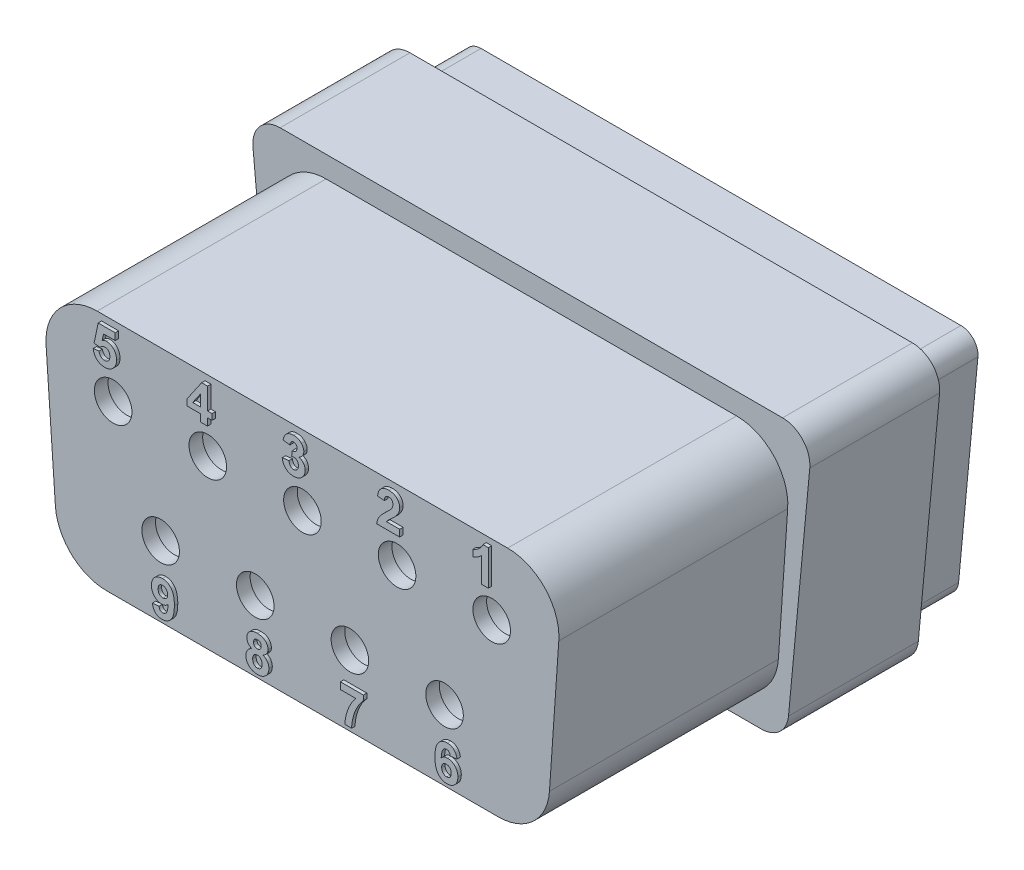
SolidWorks part; units mm, degrees
ref_plane "Front Plane" through (0, 0, 0) normal (0, 0, 1) x (1, 0, 0)
ref_plane "Top Plane" through (0, 0, 0) normal (0, 1, 0) x (1, 0, 0)
ref_plane "Right Plane" through (0, 0, 0) normal (1, 0, 0) x (0, 0, -1)
sketch "Sketch1" plane through (0, 0, 0) normal (0, 0, 1) x (1, 0, 0)
  line L0 (-7.3524, 4.1) -> (-7.3524, -7.0187) construction
  line L1 (7.3524, 4.1) -> (7.3524, -6.7915) construction
  line L4 (0, 4.1) -> (0, -4.1) construction
  line L5 (-15.42, 0) -> (15.42, 0) construction
  line L12 (7.5263, -3.3751) -> (8.1489, 3.2249)
  line L13 (-6.7298, -4.1) -> (6.7298, -4.1)
  line L14 (-8.1489, 3.2249) -> (-7.5263, -3.3751)
  line L15 (7.3524, 4.1) -> (-7.3524, 4.1)
  arc A12 (8.1489, 3.2249) -> (7.3524, 4.1) centre (7.3524, 3.3) ccw
  arc A13 (6.7298, -4.1) -> (7.5263, -3.3751) centre (6.7298, -3.3) ccw
  arc A14 (-7.5263, -3.3751) -> (-6.7298, -4.1) centre (-6.7298, -3.3) ccw
  arc A15 (-7.3524, 4.1) -> (-8.1489, 3.2249) centre (-7.3524, 3.3) ccw
  point P4 (0, 0)
  dimension "D4" = 0.8
  dimension "D1" = 16.2978
  dimension "D2" = 15.0525
  dimension "D3" = 8.2
  dimension "D5" = 4.1
  dimension "D6" = 7.5263
  dimension "D7" = 7.3524
  dimension "D8" = 5.389
  dimension "D9" = 7.3524
  dimension "D10" = 5.389
extrude "Boss-Extrude1" add sketch "Sketch1" along normal blind 3.8
sketch "Sketch2" plane through (0, 0, 0) normal (0, 0, -1) x (-1, 0, 0)
  line L0 (-9.3074, 0) -> (9.3074, 0) construction
  line L1 (0, 6.7455) -> (0, -6.1309) construction
  line L2 (-5.8958, 3.5) -> (5.8958, 3.5) construction
  line L11 (6.9289, -3.3188) -> (7.5516, 3.2812)
  line L12 (-6.7298, -3.5) -> (6.7298, -3.5)
  line L13 (7.3524, 3.5) -> (-7.3524, 3.5)
  line L14 (-7.5516, 3.2812) -> (-6.9289, -3.3188)
  line L15 (6.9546, -3.047) -> (7.5206, 2.953)
  line L16 (-6.4568, -3.5) -> (6.4568, -3.5)
  line L17 (7.0228, 3.5) -> (-7.0228, 3.5)
  line L18 (-7.5206, 2.953) -> (-6.9546, -3.047)
  arc A4 (7.5206, 2.953) -> (7.0228, 3.5) centre (7.0228, 3) ccw
  arc A5 (6.9546, -3.047) -> (6.4568, -3.5) centre (6.4568, -3) cw
  arc A6 (-6.9546, -3.047) -> (-6.4568, -3.5) centre (-6.4568, -3) ccw
  arc A7 (-7.5206, 2.953) -> (-7.0228, 3.5) centre (-7.0228, 3) cw
  arc A8 (7.5516, 3.2812) -> (7.3524, 3.5) centre (7.3524, 3.3) ccw
  arc A9 (6.7298, -3.5) -> (6.9289, -3.3188) centre (6.7298, -3.3) ccw
  arc A10 (-7.3524, 3.5) -> (-7.5516, 3.2812) centre (-7.3524, 3.3) ccw
  arc A11 (-6.9289, -3.3188) -> (-6.7298, -3.5) centre (-6.7298, -3.3) ccw
  point P2 (0, 0)
  point P8 (0, 3.5)
  dimension "D3" = 0.5
  dimension "D1" = 3.5
  dimension "D2" = 0.6
extrude "Boss-Extrude2" add sketch "Sketch2" along normal blind 1.75
sketch "Sketch3" plane through (0, 0, -1.75) normal (0, 0, -1) x (-1, 0, 0)
  line L0 (-7.8447, 0) -> (7.8447, 0) construction
  line L1 (-7.5263, -3.3751) -> (-8.1489, 3.2249) construction
  line L2 (8.1489, 3.2249) -> (7.5263, -3.3751) construction
  line L3 (7.5206, 2.953) -> (7.5206, -6.4358) construction
  line L4 (-7.5206, 2.953) -> (-7.5206, -5.6245) construction
  line L5 (2.77, 1.42) -> (5.54, 1.42) construction
  line L6 (4.155, 1.42) -> (4.155, -5.9419) construction
  circle A0 centre (5.54, 1.42) radius 0.5
  circle A1 centre (2.77, 1.42) radius 0.5
  circle A2 centre (0, 1.42) radius 0.5
  circle A3 centre (-2.77, 1.42) radius 0.5
  circle A4 centre (-5.54, 1.42) radius 0.5
  circle A5 centre (4.1506, -1.42) radius 0.5
  circle A6 centre (1.3806, -1.42) radius 0.5
  circle A7 centre (-1.3894, -1.42) radius 0.5
  circle A8 centre (-4.1594, -1.42) radius 0.5
  dimension "D2" = 1
  dimension "D14" = 1
  dimension "D1" = 1.9806
  dimension "D3" = 1.42
  dimension "D5" = 2.77
  dimension "D6" = 2.77
  dimension "D7" = 2.77
  dimension "D8" = 2.77
  dimension "D9" = 1.9806
  dimension "D10" = 3.3656
  dimension "D11" = 3.37
  dimension "D12" = 4
  dimension "D13" = 1.42
  dimension "D15" = 1.42
  dimension "D4" = 5
extrude "Cut-Extrude1" cut sketch "Sketch3" against normal up to surface (5.55 mm away) up to face at (0, -0.0321, 3.8)
sketch "Sketch6" plane through (0, 0, -1.75) normal (0, 0, -1) x (-1, 0, 0)
  line L0 (-7.4543, 2.25) -> (7.4543, 2.25) construction
  line L1 (-7.5206, 2.953) -> (-6.9546, -3.047) construction
  line L2 (6.9546, -3.047) -> (7.5206, 2.953) construction
  line L3 (7.0228, 3.5) -> (-7.0228, 3.5) construction
  line L4 (-6.9307, -3.3) -> (6.9307, -3.3) construction
  line L5 (-7.5206, 2.953) -> (-6.9546, -3.047) construction
  line L6 (-6.4568, -3.5) -> (6.4568, -3.5) construction
  text T0 "    1     2     3     4     5" font "Arial" height in points 4
  text T1 "      6     7     8     9" font "Arial" height in points 4
  dimension "D1" = 1.25
  dimension "D2" = 0.2
extrude "Boss-Extrude4" add sketch "Sketch6" along normal blind 0.1
ref_plane "Plane2" through (0, 0, 2.05) normal (0, 0, 1) x (1, 0, 0)
sketch "Sketch8" plane through (0, 0, 2.05) normal (0, 0, 1) x (1, 0, 0)
  circle A0 centre (-5.54, 1.42) radius 0.75
  circle A1 centre (-2.77, 1.42) radius 0.75
  circle A2 centre (0, 1.42) radius 0.75
  circle A3 centre (2.77, 1.42) radius 0.75
  circle A4 centre (5.54, 1.42) radius 0.75
  circle A5 centre (4.1594, -1.42) radius 0.75
  circle A6 centre (1.3894, -1.42) radius 0.75
  circle A7 centre (-1.3806, -1.42) radius 0.75
  circle A8 centre (-4.1506, -1.42) radius 0.75
  dimension "D1" = 1.5
extrude "Cut-Extrude3" cut sketch "Sketch8" against normal up to surface (3.8 mm away) up to face at (-4.099, -2.884, -1.75)
sketch "Sketch9" plane through (0, 0, 3.8) normal (0, 0, 1) x (1, 0, 0)
  line L0 (-7.5033, 1.8715) -> (-7.23, -2.0785)
  line L1 (-5.7336, -3.475) -> (5.7336, -3.475)
  line L2 (7.23, -2.0785) -> (7.5033, 1.8715)
  line L3 (6.0069, 3.475) -> (-6.0069, 3.475)
  line L4 (0, 3.475) -> (0, -3.475) construction
  line L5 (-7.3666, -0.1035) -> (7.3666, -0.1035) construction
  arc A0 (-7.23, -2.0785) -> (-5.7336, -3.475) centre (-5.7336, -1.975) ccw
  arc A1 (5.7336, -3.475) -> (7.23, -2.0785) centre (5.7336, -1.975) ccw
  arc A2 (7.5033, 1.8715) -> (6.0069, 3.475) centre (6.0069, 1.975) ccw
  arc A3 (-6.0069, 3.475) -> (-7.5033, 1.8715) centre (-6.0069, 1.975) ccw
  circle A4 centre (-5.54, 1.42) radius 0.5 construction
  circle A5 centre (-2.77, 1.42) radius 0.5 construction
  circle A6 centre (0, 1.42) radius 0.5 construction
  circle A7 centre (2.77, 1.42) radius 0.5 construction
  circle A8 centre (5.54, 1.42) radius 0.5 construction
  circle A9 centre (4.1594, -1.42) radius 0.5 construction
  circle A10 centre (1.3894, -1.42) radius 0.5 construction
  circle A11 centre (-1.3806, -1.42) radius 0.5 construction
  circle A12 centre (-4.1506, -1.42) radius 0.5 construction
  circle A13 centre (-5.54, 1.42) radius 0.5
  circle A14 centre (-2.77, 1.42) radius 0.5
  circle A15 centre (0, 1.42) radius 0.5
  circle A16 centre (2.77, 1.42) radius 0.5
  circle A17 centre (5.54, 1.42) radius 0.5
  circle A18 centre (4.1594, -1.42) radius 0.5
  circle A19 centre (1.3894, -1.42) radius 0.5
  circle A20 centre (-1.3806, -1.42) radius 0.5
  circle A21 centre (-4.1506, -1.42) radius 0.5
  dimension "D5" = 1.5
extrude "Boss-Extrude5" add sketch "Sketch9" along normal blind 6.7
sketch "Sketch10" plane through (0, 0, 10.5) normal (0, 0, 1) x (1, 0, 0)
  line L0 (-8.0522, 2.275) -> (8.0522, 2.275) construction
  line L1 (-7.5334, -3.275) -> (7.5334, -3.275) construction
  line L2 (0, 4.1751) -> (0, -4.0249) construction
  line L3 (-7.8376, 0) -> (7.8376, 0) construction
  line L4 (6.0069, 3.475) -> (-6.0069, 3.475) construction
  line L5 (-5.7336, -3.475) -> (5.7336, -3.475) construction
  text T0 "     5     4     3     2     1" font "Arial" height in points 4
  text T1 "        9     8     7     6" font "Arial" height in points 4
  dimension "D1" = 1.2
  dimension "D2" = 0.2
extrude "Boss-Extrude6" add sketch "Sketch10" along normal blind 0.1
sketch "Sketch11" plane through (0, 0, 2.05) normal (0, 0, -1) x (-1, 0, 0)
  circle A0 centre (-5.54, 1.42) radius 0.75 construction
  circle A1 centre (-2.77, 1.42) radius 0.75 construction
  circle A2 centre (0, 1.42) radius 0.75 construction
  circle A3 centre (2.77, 1.42) radius 0.75 construction
  circle A4 centre (5.54, 1.42) radius 0.75 construction
  circle A5 centre (-4.1594, -1.42) radius 0.75 construction
  circle A6 centre (-1.3894, -1.42) radius 0.75 construction
  circle A7 centre (1.3806, -1.42) radius 0.75 construction
  circle A8 centre (4.1506, -1.42) radius 0.75 construction
  circle A9 centre (-5.54, 1.42) radius 0.75
  circle A10 centre (-2.77, 1.42) radius 0.75
  circle A11 centre (0, 1.42) radius 0.75
  circle A12 centre (2.77, 1.42) radius 0.75
  circle A13 centre (5.54, 1.42) radius 0.75
  circle A14 centre (-4.1594, -1.42) radius 0.75
  circle A15 centre (-1.3894, -1.42) radius 0.75
  circle A16 centre (1.3806, -1.42) radius 0.75
  circle A17 centre (4.1506, -1.42) radius 0.75
extrude "Cut-Extrude5" cut sketch "Sketch11" against normal up to surface (8.45 mm away) up to face at (4.341, -2.6769, 10.5)
sketch "Sketch12" plane through (0, 0, 10.5) normal (0, 0, 1) x (1, 0, 0)
  circle A0 centre (-5.54, 1.42) radius 0.55
  circle A1 centre (-2.77, 1.42) radius 0.55
  circle A2 centre (0, 1.42) radius 0.55
  circle A3 centre (2.77, 1.42) radius 0.55
  circle A4 centre (5.54, 1.42) radius 0.55
  circle A5 centre (4.1594, -1.42) radius 0.55
  circle A6 centre (1.3894, -1.42) radius 0.55
  circle A7 centre (-1.3806, -1.42) radius 0.55
  circle A8 centre (-4.1506, -1.42) radius 0.55
  circle A9 centre (-5.54, 1.42) radius 0.75 construction
  circle A10 centre (-5.54, 1.42) radius 0.75
  circle A11 centre (-2.77, 1.42) radius 0.75 construction
  circle A12 centre (0, 1.42) radius 0.75 construction
  circle A13 centre (2.77, 1.42) radius 0.75 construction
  circle A14 centre (5.54, 1.42) radius 0.75 construction
  circle A15 centre (-2.77, 1.42) radius 0.75
  circle A16 centre (0, 1.42) radius 0.75
  circle A17 centre (2.77, 1.42) radius 0.75
  circle A18 centre (5.54, 1.42) radius 0.75
  circle A19 centre (-4.1506, -1.42) radius 0.75 construction
  circle A20 centre (-1.3806, -1.42) radius 0.75 construction
  circle A21 centre (1.3894, -1.42) radius 0.75 construction
  circle A22 centre (4.1594, -1.42) radius 0.75 construction
  circle A23 centre (-4.1506, -1.42) radius 0.75
  circle A24 centre (-1.3806, -1.42) radius 0.75
  circle A25 centre (1.3894, -1.42) radius 0.75
  circle A26 centre (4.1594, -1.42) radius 0.75
  dimension "D1" = 1.1
extrude "Boss-Extrude7" add sketch "Sketch12" against normal blind 0.4
